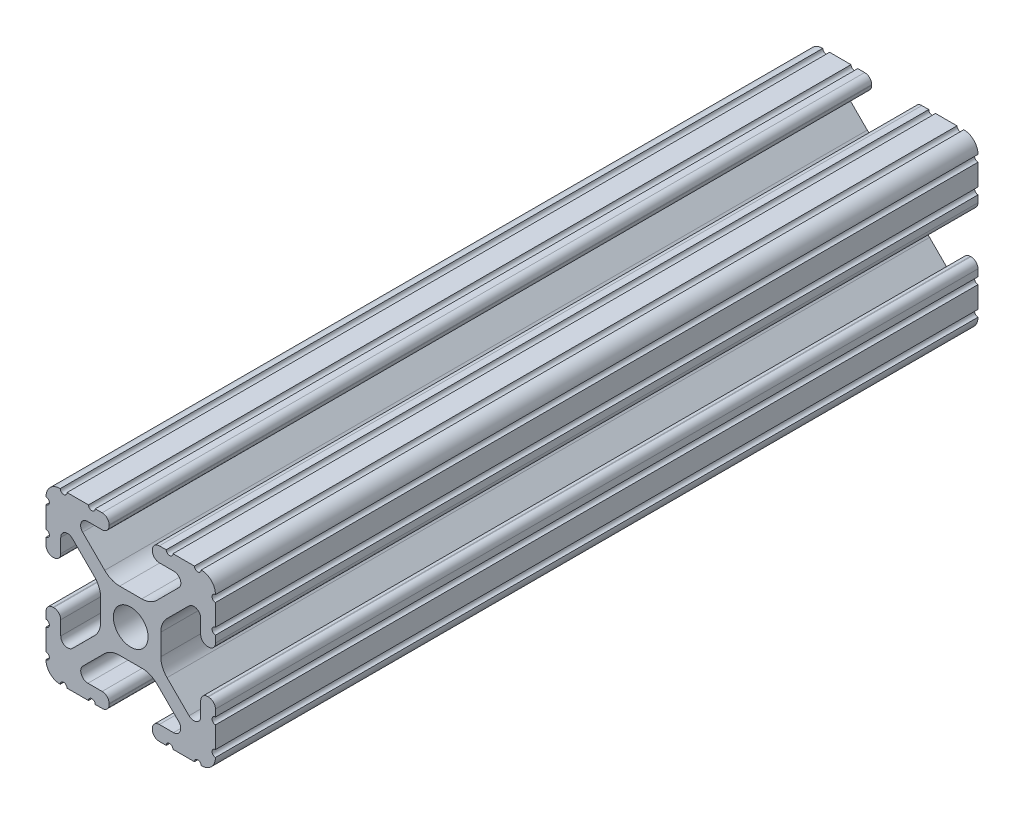
SolidWorks part; units mm, degrees
ref_plane "Front Plane" through (0, 0, 0) normal (0, 0, 1) x (1, 0, 0)
ref_plane "Top Plane" through (0, 0, 0) normal (0, 1, 0) x (1, 0, 0)
ref_plane "Right Plane" through (0, 0, 0) normal (1, 0, 0) x (0, 0, -1)
sketch "Sketch1" plane through (0, 0, 0) normal (0, 0, 1) x (1, 0, 0)
  line L88 (-7.1797, -8.6452) -> (-3.9523, -5.4237)
  line L89 (-1.7093, -4.4958) -> (1.7093, -4.4958)
  line L90 (3.9523, -5.4237) -> (7.1797, -8.6452)
  line L91 (6.4164, -10.4902) -> (4.2875, -10.4902)
  line L92 (3.2385, -11.5392) -> (3.2385, -11.651)
  line L93 (4.2875, -12.7) -> (5.3171, -12.7)
  line L94 (6.3331, -12.7) -> (9.5504, -12.7)
  line L95 (12.7, -9.5504) -> (12.7, -6.3331)
  line L96 (12.7, -5.3171) -> (12.7, -4.2875)
  line L97 (11.651, -3.2385) -> (11.5392, -3.2385)
  line L98 (10.4902, -4.2875) -> (10.4902, -6.4021)
  line L99 (8.7371, -7.1294) -> (5.441, -3.8408)
  line L100 (4.5085, -1.5932) -> (4.5085, 1.5932)
  line L101 (5.441, 3.8408) -> (8.7371, 7.1294)
  line L102 (10.4902, 6.4021) -> (10.4902, 4.2875)
  line L103 (11.5392, 3.2385) -> (11.651, 3.2385)
  line L104 (12.7, 4.2875) -> (12.7, 5.3171)
  line L105 (12.7, 6.3331) -> (12.7, 9.5504)
  line L106 (9.5504, 12.7) -> (6.3331, 12.7)
  line L107 (5.3171, 12.7) -> (4.2875, 12.7)
  line L108 (3.2385, 11.651) -> (3.2385, 11.5392)
  line L109 (4.2875, 10.4902) -> (6.4768, 10.4902)
  line L110 (7.207, 8.7244) -> (3.8983, 5.4232)
  line L111 (1.6558, 4.4958) -> (-1.6558, 4.4958)
  line L112 (-3.8983, 5.4232) -> (-7.207, 8.7244)
  line L113 (-6.4768, 10.4902) -> (-4.2875, 10.4902)
  line L114 (-3.2385, 11.5392) -> (-3.2385, 11.651)
  line L115 (-4.2875, 12.7) -> (-5.3171, 12.7)
  line L116 (-6.3331, 12.7) -> (-9.5504, 12.7)
  line L117 (-12.7, 9.5504) -> (-12.7, 6.3331)
  line L118 (-12.7, 5.3171) -> (-12.7, 4.2875)
  line L119 (-11.651, 3.2385) -> (-11.5392, 3.2385)
  line L120 (-10.4902, 4.2875) -> (-10.4902, 6.4021)
  line L121 (-8.7371, 7.1294) -> (-5.441, 3.8408)
  line L122 (-4.5085, 1.5932) -> (-4.5085, -1.5932)
  line L123 (-5.441, -3.8408) -> (-8.7371, -7.1294)
  line L124 (-10.4902, -6.4021) -> (-10.4902, -4.2875)
  line L125 (-11.5392, -3.2385) -> (-11.651, -3.2385)
  line L126 (-12.7, -4.2875) -> (-12.7, -5.3171)
  line L127 (-12.7, -6.3331) -> (-12.7, -9.5504)
  line L128 (-9.5504, -12.7) -> (-6.3331, -12.7)
  line L129 (-5.3171, -12.7) -> (-4.2875, -12.7)
  line L130 (-3.2385, -11.651) -> (-3.2385, -11.5392)
  line L131 (-4.2875, -10.4902) -> (-6.4164, -10.4902)
  circle A1 centre (0, 0) radius 2.6035
  arc A104 (-7.1797, -8.6452) -> (-6.4164, -10.4902) centre (-6.4164, -9.4098) ccw
  arc A105 (-1.7093, -4.4958) -> (-3.9523, -5.4237) centre (-1.7093, -7.6708) ccw
  arc A106 (3.9523, -5.4237) -> (1.7093, -4.4958) centre (1.7093, -7.6708) ccw
  arc A107 (6.4164, -10.4902) -> (7.1797, -8.6452) centre (6.4164, -9.4098) ccw
  arc A108 (4.2875, -10.4902) -> (3.2385, -11.5392) centre (4.2875, -11.5392) ccw
  arc A109 (3.2385, -11.651) -> (4.2875, -12.7) centre (4.2875, -11.651) ccw
  arc A110 (6.3331, -12.7) -> (5.3171, -12.7) centre (5.8251, -12.7) ccw
  arc A111 (10.5664, -12.6998) -> (9.5504, -12.7) centre (10.0584, -12.7) ccw
  arc A112 (10.5664, -12.6998) -> (12.6998, -10.5664) centre (10.5918, -10.5918) ccw
  arc A113 (12.7, -9.5504) -> (12.6998, -10.5664) centre (12.7, -10.0584) ccw
  arc A114 (12.7, -5.3171) -> (12.7, -6.3331) centre (12.7, -5.8251) ccw
  arc A115 (12.7, -4.2875) -> (11.651, -3.2385) centre (11.651, -4.2875) ccw
  arc A116 (11.5392, -3.2385) -> (10.4902, -4.2875) centre (11.5392, -4.2875) ccw
  arc A117 (8.7371, -7.1294) -> (10.4902, -6.4021) centre (9.4628, -6.4021) ccw
  arc A118 (4.5085, -1.5932) -> (5.441, -3.8408) centre (7.6835, -1.5932) ccw
  arc A119 (5.441, 3.8408) -> (4.5085, 1.5932) centre (7.6835, 1.5932) ccw
  arc A120 (10.4902, 6.4021) -> (8.7371, 7.1294) centre (9.4628, 6.4021) ccw
  arc A121 (10.4902, 4.2875) -> (11.5392, 3.2385) centre (11.5392, 4.2875) ccw
  arc A122 (11.651, 3.2385) -> (12.7, 4.2875) centre (11.651, 4.2875) ccw
  arc A123 (12.7, 6.3331) -> (12.7, 5.3171) centre (12.7, 5.8251) ccw
  arc A124 (12.6998, 10.5664) -> (12.7, 9.5504) centre (12.7, 10.0584) ccw
  arc A125 (12.6998, 10.5664) -> (10.5664, 12.6998) centre (10.5918, 10.5918) ccw
  arc A126 (9.5504, 12.7) -> (10.5664, 12.6998) centre (10.0584, 12.7) ccw
  arc A127 (5.3171, 12.7) -> (6.3331, 12.7) centre (5.8251, 12.7) ccw
  arc A128 (4.2875, 12.7) -> (3.2385, 11.651) centre (4.2875, 11.651) ccw
  arc A129 (3.2385, 11.5392) -> (4.2875, 10.4902) centre (4.2875, 11.5392) ccw
  arc A130 (7.207, 8.7244) -> (6.4768, 10.4902) centre (6.4768, 9.4563) ccw
  arc A131 (1.6558, 4.4958) -> (3.8983, 5.4232) centre (1.6558, 7.6708) ccw
  arc A132 (-3.8983, 5.4232) -> (-1.6558, 4.4958) centre (-1.6558, 7.6708) ccw
  arc A133 (-6.4768, 10.4902) -> (-7.207, 8.7244) centre (-6.4768, 9.4563) ccw
  arc A134 (-4.2875, 10.4902) -> (-3.2385, 11.5392) centre (-4.2875, 11.5392) ccw
  arc A135 (-3.2385, 11.651) -> (-4.2875, 12.7) centre (-4.2875, 11.651) ccw
  arc A136 (-6.3331, 12.7) -> (-5.3171, 12.7) centre (-5.8251, 12.7) ccw
  arc A137 (-10.5664, 12.6998) -> (-9.5504, 12.7) centre (-10.0584, 12.7) ccw
  arc A138 (-10.5664, 12.6998) -> (-12.6998, 10.5664) centre (-10.5918, 10.5918) ccw
  arc A139 (-12.7, 9.5504) -> (-12.6998, 10.5664) centre (-12.7, 10.0584) ccw
  arc A140 (-12.7, 5.3171) -> (-12.7, 6.3331) centre (-12.7, 5.8251) ccw
  arc A141 (-12.7, 4.2875) -> (-11.651, 3.2385) centre (-11.651, 4.2875) ccw
  arc A142 (-11.5392, 3.2385) -> (-10.4902, 4.2875) centre (-11.5392, 4.2875) ccw
  arc A143 (-8.7371, 7.1294) -> (-10.4902, 6.4021) centre (-9.4628, 6.4021) ccw
  arc A144 (-4.5085, 1.5932) -> (-5.441, 3.8408) centre (-7.6835, 1.5932) ccw
  arc A145 (-5.441, -3.8408) -> (-4.5085, -1.5932) centre (-7.6835, -1.5932) ccw
  arc A146 (-10.4902, -6.4021) -> (-8.7371, -7.1294) centre (-9.4628, -6.4021) ccw
  arc A147 (-10.4902, -4.2875) -> (-11.5392, -3.2385) centre (-11.5392, -4.2875) ccw
  arc A148 (-11.651, -3.2385) -> (-12.7, -4.2875) centre (-11.651, -4.2875) ccw
  arc A149 (-12.7, -6.3331) -> (-12.7, -5.3171) centre (-12.7, -5.8251) ccw
  arc A150 (-12.6998, -10.5664) -> (-12.7, -9.5504) centre (-12.7, -10.0584) ccw
  arc A151 (-12.6998, -10.5664) -> (-10.5664, -12.6998) centre (-10.5918, -10.5918) ccw
  arc A152 (-9.5504, -12.7) -> (-10.5664, -12.6998) centre (-10.0584, -12.7) ccw
  arc A153 (-5.3171, -12.7) -> (-6.3331, -12.7) centre (-5.8251, -12.7) ccw
  arc A154 (-4.2875, -12.7) -> (-3.2385, -11.651) centre (-4.2875, -11.651) ccw
  arc A155 (-3.2385, -11.5392) -> (-4.2875, -10.4902) centre (-4.2875, -11.5392) ccw
extrude "Boss-Extrude1" add sketch "Sketch1" along normal mid plane 114.3
